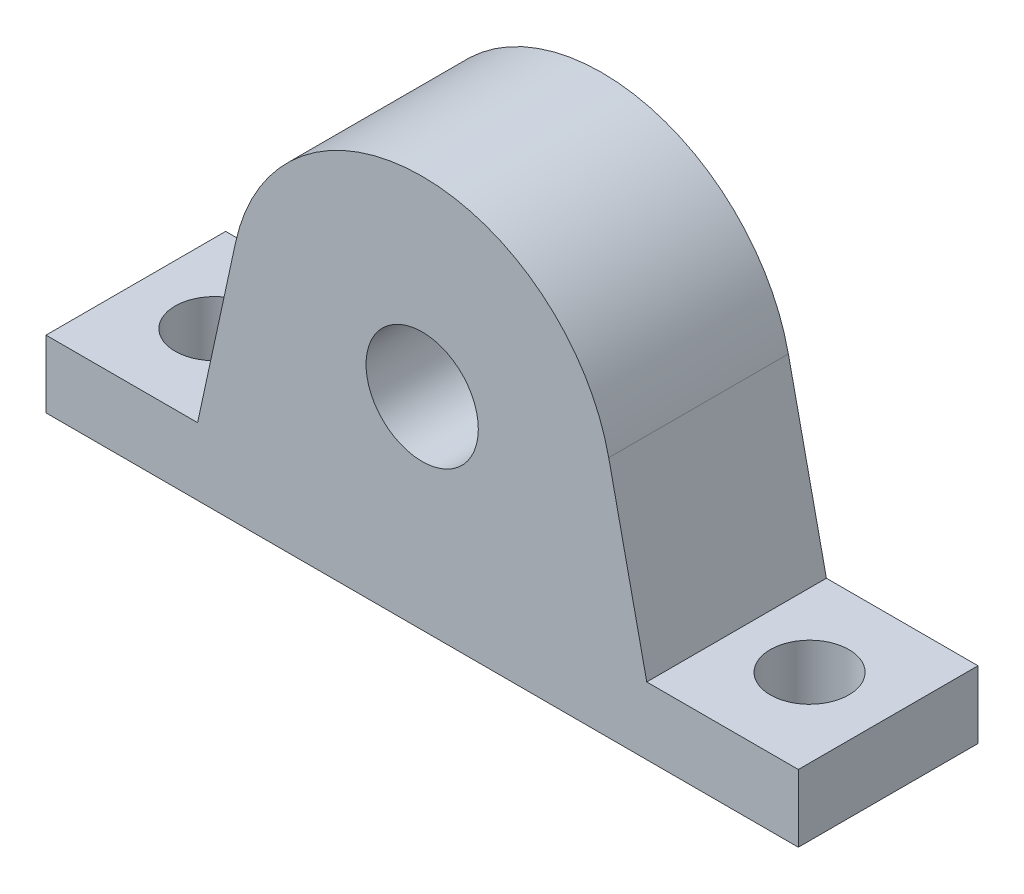
SolidWorks part; units mm, degrees
ref_plane "前视基准面" through (0, 0, 0) normal (0, 0, 1) x (1, 0, 0)
ref_plane "上视基准面" through (0, 0, 0) normal (0, 1, 0) x (1, 0, 0)
ref_plane "右视基准面" through (0, 0, 0) normal (1, 0, 0) x (0, 0, -1)
sketch "草图1" plane through (0, 0, 0) normal (0, 0, 1) x (1, 0, 0)
  line L0 (0, -11.7144) -> (0, 40.3286) construction
  line L1 (-33.5, 0) -> (33.5, 0)
  line L2 (-33.5, 0) -> (-33.5, 6)
  line L3 (-33.5, 6) -> (-20, 6)
  line L4 (-20, 6) -> (-16.6133, 21.6054)
  line L5 (20, 6) -> (16.6133, 21.6054)
  line L6 (33.5, 6) -> (20, 6)
  line L7 (33.5, 0) -> (33.5, 6)
  arc A0 (-16.6133, 21.6054) -> (16.6133, 21.6054) centre (0, 18) cw
  point P4 (0, 40.3286)
  point P13 (0, 0)
  point P14 (16.4951, 21.6857)
  dimension "D1" = 67
  dimension "D3" = 35
  dimension "D2" = 6
  dimension "D4" = 18
  dimension "D5" = 13.5
extrude "凸台-拉伸1" add sketch "草图1" along normal mid plane 16
sketch "草图2" plane through (0, 6, 0) normal (0, 1, 0) x (1, 0, 0)
  line L0 (0, 0) -> (0, 23.5984) construction
  circle A0 centre (-26.5, 0) radius 3.5
  circle A1 centre (26.5, 0) radius 3.5
  point P7 (0, 0)
  dimension "D1" = 7
  dimension "D2" = 7
  dimension "D3" = 53
extrude "切除-拉伸1" cut sketch "草图2" against normal blind 16
sketch "草图3" plane through (0, 0, 8) normal (0, 0, 1) x (1, 0, 0)
  circle A0 centre (0, 18) radius 5
  dimension "D1" = 10
extrude "切除-拉伸2" cut sketch "草图3" against normal blind 16
